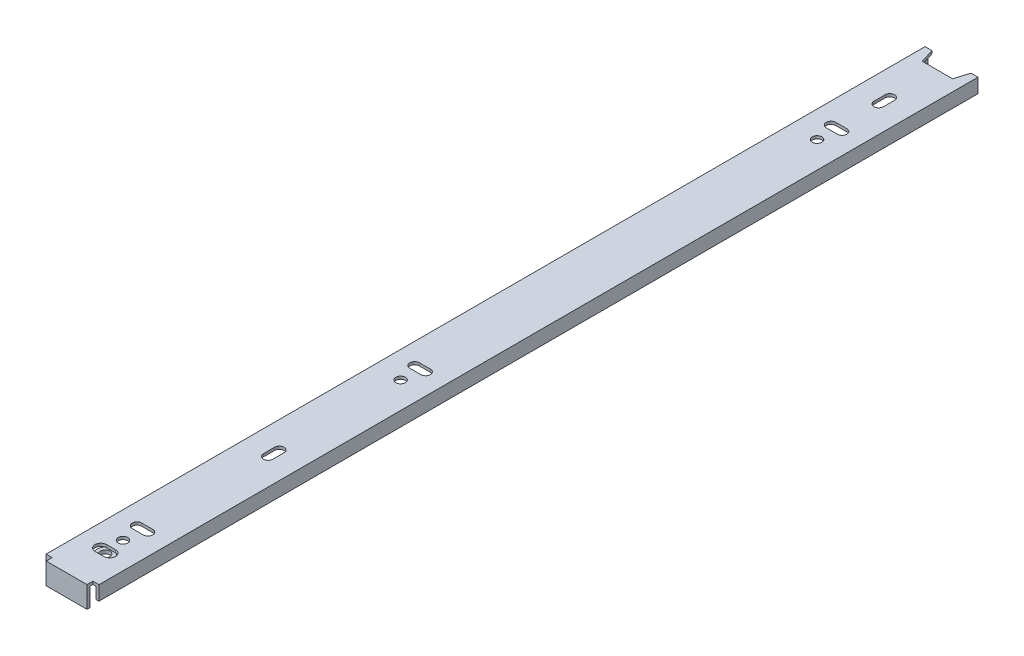
SolidWorks part; units mm, degrees
ref_plane "Front Plane" through (0, 0, 0) normal (0, 0, 1) x (1, 0, 0)
ref_plane "Top Plane" through (0, 0, 0) normal (0, 1, 0) x (1, 0, 0)
ref_plane "Right Plane" through (0, 0, 0) normal (1, 0, 0) x (0, 0, -1)
ref_plane "Plane1" through (0, -0.6, 0) normal (0, -1, 0) x (1, 0, 0)
sketch "Sketch1" plane through (0, -0.6, 0) normal (0, -1, 0) x (1, 0, 0)
  line L0 (3.75, 390.2) -> (3.1403, 397.9471)
  line L1 (-3.1403, 397.9471) -> (-3.75, 390.2)
  arc A0 (3.1403, 397.9471) -> (-3.1403, 397.9471) centre (0, 397.7) ccw
  arc A1 (-3.75, 390.2) -> (3.75, 390.2) centre (0, 390.2) ccw
extrude "Boss-Extrude1" add sketch "Sketch1" against normal blind 2.6
ref_plane "Plane2" through (0, 2, 0) normal (0, -1, 0) x (1, 0, 0)
sketch "Sketch2" plane through (0, 2, 0) normal (0, -1, 0) x (1, 0, 0)
  line L0 (-12.2, 408) -> (-12.2, 0)
  line L1 (-12.2, 0) -> (12.2, 0)
  line L2 (12.2, 0) -> (12.2, 408)
  line L3 (12.2, 408) -> (-12.2, 408)
  line L4 (-2.05, 392.9) -> (2.05, 392.9)
  line L5 (2.05, 387.5) -> (-2.05, 387.5)
  arc A0 (-2.05, 387.5) -> (-2.05, 392.9) centre (-2.05, 390.2) cw
  arc A1 (2.05, 392.9) -> (2.05, 387.5) centre (2.05, 390.2) cw
extrude "Boss-Extrude2" add sketch "Sketch2" against normal blind 1.3
sketch "Sketch3" plane through (0, 3.3, 0) normal (0, 1, 0) x (-1, 0, 0)
  line L0 (-12.2, 405.3) -> (-9.4, 405.3)
  line L1 (-9.4, 405.3) -> (-9.4, 408)
  line L2 (-9.4, 408) -> (-12.2, 408)
  line L3 (-12.2, 408) -> (-12.2, 405.3)
extrude "Cut-Extrude1" cut sketch "Sketch3" against normal through all
sketch "Sketch4" plane through (0, 2, 0) normal (0, -1, 0) x (1, 0, 0)
  line L0 (12.2, 0) -> (10.9, 0)
  line L1 (10.9, 0) -> (10.9, 405.3)
  line L2 (10.9, 405.3) -> (12.2, 405.3)
  line L3 (12.2, 405.3) -> (12.2, 0)
extrude "Boss-Extrude3" add sketch "Sketch4" along normal blind 5.3
sketch "Sketch5" plane through (0, 3.3, 0) normal (0, 1, 0) x (-1, 0, 0)
  line L0 (9.4, 405.3) -> (12.2, 405.3)
  line L1 (12.2, 405.3) -> (12.2, 408)
  line L2 (12.2, 408) -> (9.4, 408)
  line L3 (9.4, 408) -> (9.4, 405.3)
extrude "Cut-Extrude2" cut sketch "Sketch5" against normal through all
sketch "Sketch6" plane through (0, 2, 0) normal (0, -1, 0) x (1, 0, 0)
  line L0 (-10.9, 0) -> (-12.2, 0)
  line L1 (-12.2, 0) -> (-12.2, 405.3)
  line L2 (-12.2, 405.3) -> (-10.9, 405.3)
  line L3 (-10.9, 405.3) -> (-10.9, 0)
extrude "Boss-Extrude4" add sketch "Sketch6" along normal blind 5.3
sketch "Sketch7" plane through (0, 2, 0) normal (0, -1, 0) x (1, 0, 0)
  line L0 (-9.4, 406.6) -> (-9.4, 408)
  line L1 (-9.4, 408) -> (9.4, 408)
  line L2 (9.4, 408) -> (9.4, 406.6)
  line L3 (9.4, 406.6) -> (-9.4, 406.6)
extrude "Boss-Extrude5" add sketch "Sketch7" along normal blind 8.6
sketch "Sketch8" plane through (0, 3.3, 0) normal (0, 1, 0) x (-1, 0, 0)
  line L0 (-7, 0) -> (7, 0)
  line L1 (7, 0) -> (7, 6.5)
  line L2 (7, 6.5) -> (-7, 6.5)
  line L3 (-7, 6.5) -> (-7, 0)
extrude "Cut-Extrude3" cut sketch "Sketch8" against normal through all
sketch "Sketch9" plane through (0, 2, 0) normal (0, -1, 0) x (1, 0, 0)
  line L0 (2.55, 375.2) -> (-2.55, 375.2)
  line L1 (-2.55, 370.8) -> (2.55, 370.8)
  arc A0 (-2.55, 375.2) -> (-2.55, 370.8) centre (-2.55, 373) ccw
  arc A1 (2.55, 370.8) -> (2.55, 375.2) centre (2.55, 373) ccw
extrude "Cut-Extrude4" cut sketch "Sketch9" against normal through all
sketch "Sketch10" plane through (0, 2, 0) normal (0, -1, 0) x (1, 0, 0)
  line L0 (-2.5499, 242.8) -> (2.5501, 242.8)
  line L1 (2.5501, 247.2) -> (-2.5499, 247.2)
  arc A0 (2.5501, 242.8) -> (2.5501, 247.2) centre (2.5501, 245) ccw
  arc A1 (-2.5499, 247.2) -> (-2.5499, 242.8) centre (-2.5499, 245) ccw
extrude "Cut-Extrude5" cut sketch "Sketch10" against normal through all
sketch "Sketch11" plane through (0, 2, 0) normal (0, -1, 0) x (1, 0, 0)
  line L0 (2.2001, 309.95) -> (2.2001, 315.05)
  line L1 (-2.1999, 315.05) -> (-2.1999, 309.95)
  arc A0 (-2.1999, 309.95) -> (2.2001, 309.95) centre (0.0001, 309.95) ccw
  arc A1 (2.2001, 315.05) -> (-2.1999, 315.05) centre (0.0001, 315.05) ccw
extrude "Cut-Extrude6" cut sketch "Sketch11" against normal through all
sketch "Sketch12" plane through (0, 2, 0) normal (0, -1, 0) x (1, 0, 0)
  line L0 (2.2001, 28.45) -> (2.2001, 33.55)
  line L1 (-2.1999, 33.55) -> (-2.1999, 28.45)
  arc A0 (-2.1999, 28.45) -> (2.2001, 28.45) centre (0.0001, 28.45) ccw
  arc A1 (2.2001, 33.55) -> (-2.1999, 33.55) centre (0.0001, 33.55) ccw
extrude "Cut-Extrude7" cut sketch "Sketch12" against normal through all
sketch "Sketch13" plane through (0, 3.3, 0) normal (0, 1, 0) x (-1, 0, 0)
  line L0 (2.5499, 55.2) -> (-2.5501, 55.2)
  line L1 (-2.5501, 50.8) -> (2.5499, 50.8)
  arc A0 (-2.5501, 55.2) -> (-2.5501, 50.8) centre (-2.5501, 53) ccw
  arc A1 (2.5499, 50.8) -> (2.5499, 55.2) centre (2.5499, 53) ccw
extrude "Cut-Extrude8" cut sketch "Sketch13" against normal through all
sketch "Sketch14" plane through (0, -0.6, 0) normal (0, -1, 0) x (1, 0, 0)
  line L0 (0.6, 397.1) -> (2.2, 397.1)
  line L1 (2.2, 397.1) -> (2.2, 398.3)
  line L2 (2.2, 398.3) -> (0.6, 398.3)
  line L3 (0.6, 398.3) -> (0.6, 399.9)
  line L4 (0.6, 399.9) -> (-0.6, 399.9)
  line L5 (-0.6, 399.9) -> (-0.6, 398.3)
  line L6 (-0.6, 398.3) -> (-2.2, 398.3)
  line L7 (-2.2, 398.3) -> (-2.2, 397.1)
  line L8 (-2.2, 397.1) -> (-0.6, 397.1)
  line L9 (-0.6, 397.1) -> (-0.6, 395.5)
  line L10 (-0.6, 395.5) -> (0.6, 395.5)
  line L11 (0.6, 395.5) -> (0.6, 397.1)
extrude "Cut-Extrude9" cut sketch "Sketch14" against normal blind 2.6
draft "Draft1" type of draft neutral plane draft angle 17.103 faces to draft 2 face at (-7, 2.65, 3.25) face at (7, 2.65, 3.25) neutral plane through (-7, -6.6, 6.5) neutral plane normal (0, 0, -1) parameters "D1"=17.103
hole_wizard "Ø4.4 (4.4) Diameter Hole1" positions "Sketch16" profile "Sketch15" hole size "Ø4.4" standard "ANSI Metric"
sketch "Sketch16" plane through (0, 2, 0) normal (0, -1, 0) x (-1, 0, 0)
  point P0 (-0.0001, -62)
  point P1 (-0.0001, -254)
  point P2 (0, -382)
sketch "Sketch15" plane through (0.0001, 2, 62) normal (1, 0, 0) x (0, 0, -1)
  line L0 (0, 0) -> (0, 1.3)
  line L1 (0, 1.3) -> (2.2, 1.3)
  line L2 (2.2, 1.3) -> (2.2, 0)
  line L5 (2.2, 0) -> (0, 0)
  line L11 (0, -6.35) -> (0, 107.95) construction
  dimension "Thru Hole Dia." = 4.4
  dimension "Thru Hole Depth" = 1.3
hole_wizard "CBORE for M4 Hex Head Machine Screw1" positions "Sketch18" profile "Sketch17" counterbore size "M4" standard "ANSI Metric"
sketch "Sketch18" plane through (0, -0.6, 0) normal (0, -1, 0) x (-1, 0, 0)
  point P0 (0, -390.2)
sketch "Sketch17" plane through (0, -0.6, 390.2) normal (1, 0, 0) x (0, 0, -1)
  line L0 (0, 0) -> (0, 3.9)
  line L1 (0, 3.9) -> (2.2, 3.9)
  line L3 (2.2, 3.9) -> (2.2, 1)
  line L4 (2.2, 1) -> (3.75, 1)
  line L5 (3.75, 1) -> (3.75, 0)
  line L7 (3.75, 0) -> (0, 0)
  line L11 (0, -6.35) -> (0, 107.95) construction
  dimension "Thru Hole Dia." = 4.4
  dimension "Thru Hole Depth" = 3.9
  dimension "C'Bore Dia." = 7.5
  dimension "C'Bore Depth" = 1
scale "Scale1" scale about centroid uniform scaling yes scale factor 0.25
